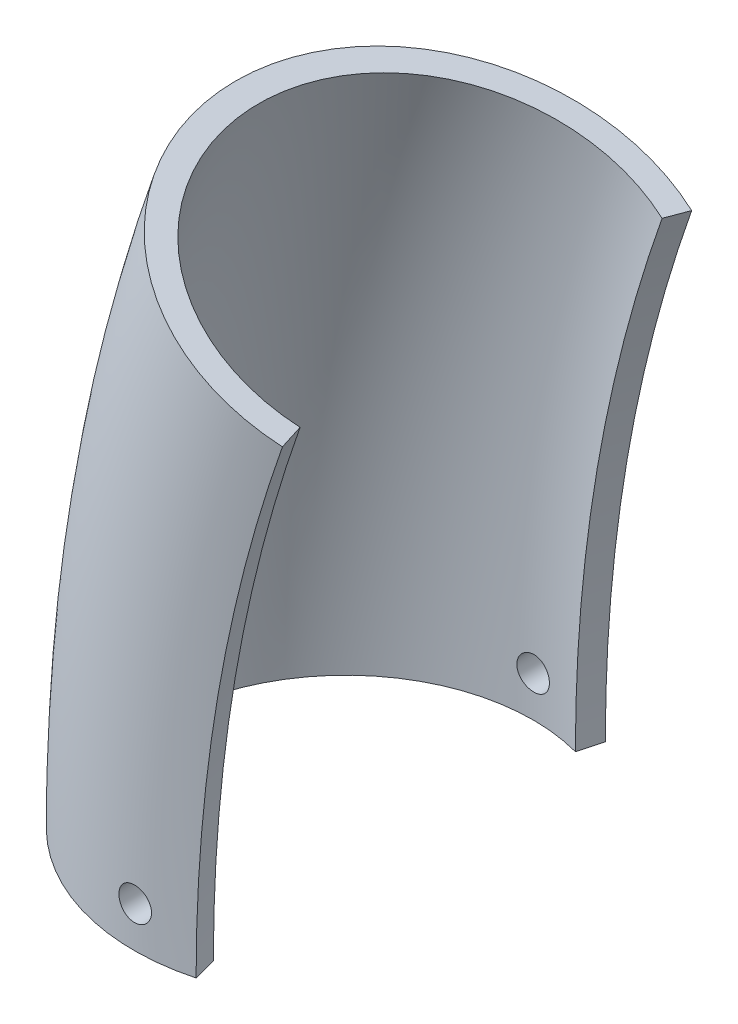
SolidWorks part; units mm, degrees
material "Plain Carbon Steel"
ref_plane "Front Plane" through (0, 0, 0) normal (0, 0, 1) x (1, 0, 0)
ref_plane "Top Plane" through (0, 0, 0) normal (0, 1, 0) x (1, 0, 0)
ref_plane "Right Plane" through (0, 0, 0) normal (1, 0, 0) x (0, 0, -1)
sketch "Sketch1" plane through (0, 0, 0) normal (0, 0, 1) x (1, 0, 0)
  arc A0 (0, 0) -> (34.8636, 203.2) centre (609.6, 0) cw
  dimension "D1" = 609.6
  dimension "D2" = 203.2
sketch "Sketch2" plane through (0, 0, 0) normal (0, 1, 0) x (1, 0, 0)
  line L0 (18.9003, -70.5367) -> (21.3655, -79.7372)
  line L1 (18.9003, 70.5367) -> (21.3655, 79.7372)
  line L2 (0, 0) -> (34.8636, 0) construction
  arc A0 (18.9003, 70.5367) -> (18.9003, -70.5367) centre (0, 0) ccw
  arc A1 (21.3655, 79.7372) -> (21.3655, -79.7372) centre (0, 0) ccw
  dimension "D1" = 73.025
  dimension "D2" = 82.55
  dimension "D3" = 150
  dimension "D4" = 75
sweep "Sweep1" add profiles "Sketch2" path "Sketch1"
sketch "Sketch3" plane through (0, 0, 0) normal (0, 0, 1) x (1, 0, 0)
  circle A0 centre (0.2067, 15.875) radius 6.35
  arc A1 (34.8636, 203.2) -> (0, 0) centre (609.6, 0) ccw construction
  dimension "D1" = 12.7
  dimension "D2" = 15.875
extrude "Cut-Extrude1" cut sketch "Sketch3" against normal through all both and the other way through all
